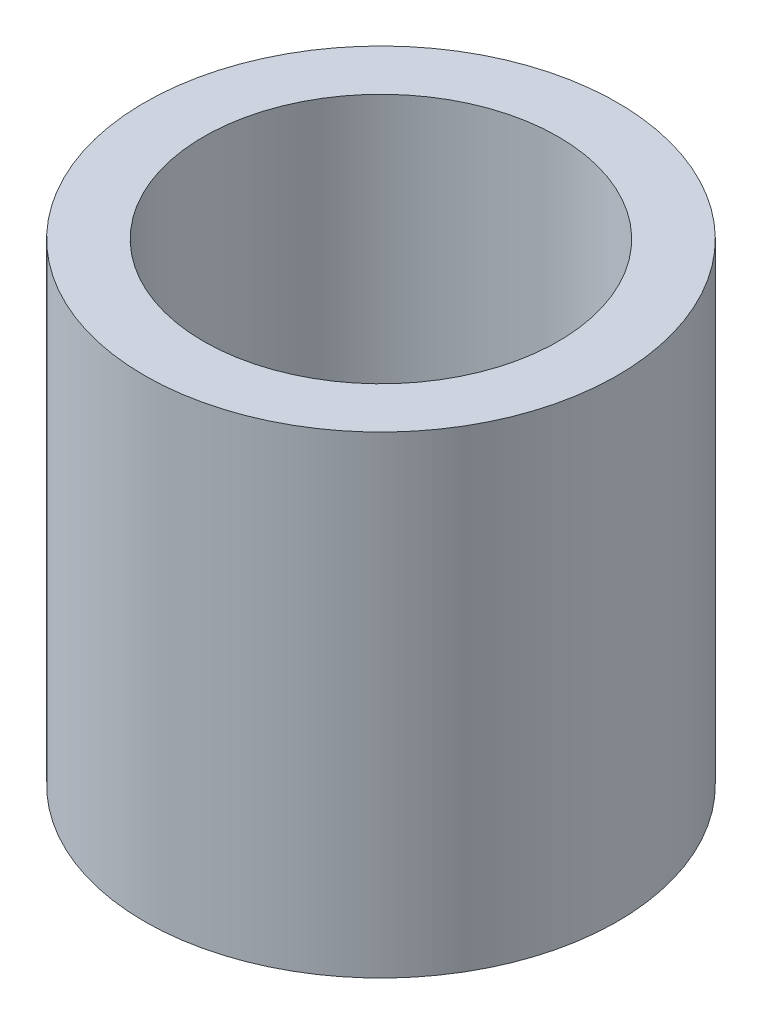
SolidWorks part; units mm, degrees
ref_plane "前视基准面" through (0, 0, 0) normal (0, 0, 1) x (1, 0, 0)
ref_plane "上视基准面" through (0, 0, 0) normal (0, 1, 0) x (1, 0, 0)
ref_plane "右视基准面" through (0, 0, 0) normal (1, 0, 0) x (0, 0, -1)
sketch "草图2" plane through (0, 0, 0) normal (0, 1, 0) x (1, 0, 0)
  circle A0 centre (0, 0) radius 7.5
  circle A1 centre (0, 0) radius 10
  dimension "D1" = 15
  dimension "D2" = 20
extrude "凸台-拉伸1" add sketch "草图2" along normal mid plane 20
